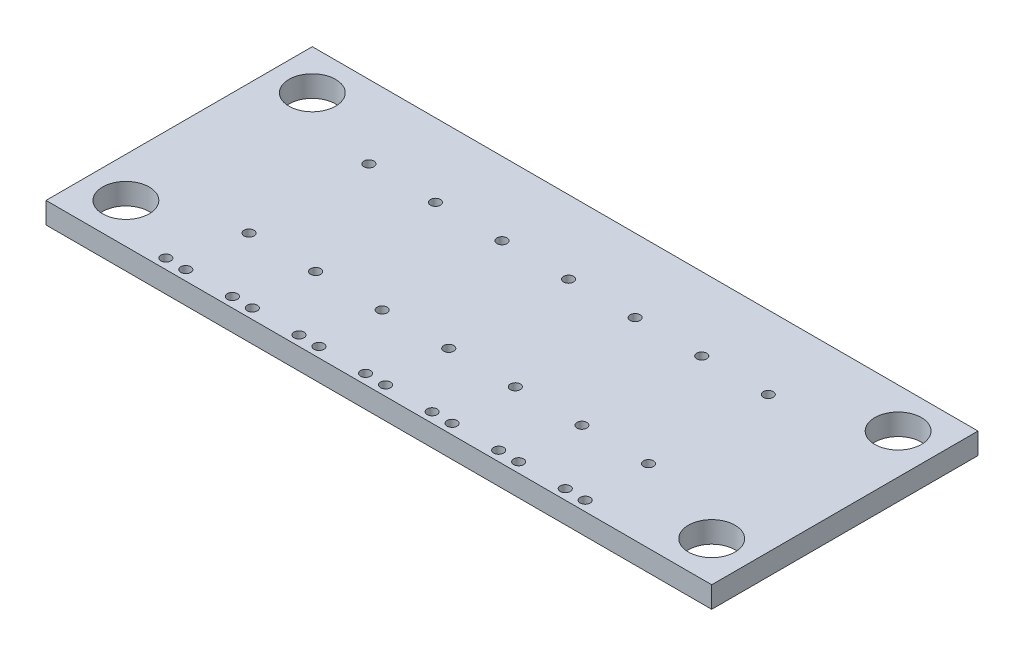
SolidWorks part; units mm, degrees
ref_plane "Front Plane" through (0, 0, 0) normal (0, 0, 1) x (1, 0, 0)
ref_plane "Top Plane" through (0, 0, 0) normal (0, 1, 0) x (1, 0, 0)
ref_plane "Right Plane" through (0, 0, 0) normal (1, 0, 0) x (0, 0, -1)
sketch "Sketch1" plane through (0, 0, 0) normal (0, 1, 0) x (1, 0, 0)
  line L1 (0, 0) -> (50, 0)
  line L2 (0, 0) -> (0, 20)
  line L3 (0, 20) -> (50, 20)
  line L4 (50, 0) -> (50, 20)
  circle A0 centre (3, 17) radius 1.75
  circle A1 centre (47, 3) radius 1.75
  circle A2 centre (3, 3) radius 1.75
  circle A3 centre (47, 17) radius 1.75
  dimension "D3" = 3.5
  dimension "D1" = 20
  dimension "D2" = 50
  dimension "D4" = 3
  dimension "D5" = 3
  dimension "D7" = 3
  dimension "D8" = 3
extrude "Boss-Extrude1" add sketch "Sketch1" along normal blind 1.6
sketch "Sketch2" plane through (0, 1.6, 0) normal (0, 1, 0) x (1, 0, 0)
  line L0 (50, 20) -> (0, 20) construction
  line L2 (7.5, 20) -> (7.5, 0)
  line L4 (10.5, 20) -> (10.5, 0)
  line L5 (0, 0) -> (50, 0) construction
  line L6 (0, 20) -> (0, 0) construction
  line L7 (9, 0) -> (9, 19.5)
  line L8 (9, 19.5) -> (7.5, 19.5)
  line L9 (10.5, 10) -> (9, 10)
  line L10 (12.5, 20) -> (12.5, 0)
  line L11 (14, 0) -> (14, 19.5)
  line L12 (15.5, 20) -> (15.5, 0)
  line L13 (15.5, 10) -> (14, 10)
  line L14 (14, 19.5) -> (12.5, 19.5)
  line L15 (17.5, 20) -> (17.5, 0)
  line L16 (19, 0) -> (19, 19.5)
  line L17 (20.5, 20) -> (20.5, 0)
  line L18 (20.5, 10) -> (19, 10)
  line L19 (19, 19.5) -> (17.5, 19.5)
  line L20 (22.5, 20) -> (22.5, 0)
  line L21 (24, 0) -> (24, 19.5)
  line L22 (25.5, 20) -> (25.5, 0)
  line L23 (25.5, 10) -> (24, 10)
  line L24 (24, 19.5) -> (22.5, 19.5)
  line L25 (27.5, 20) -> (27.5, 0)
  line L26 (29, 0) -> (29, 19.5)
  line L27 (30.5, 20) -> (30.5, 0)
  line L28 (30.5, 10) -> (29, 10)
  line L29 (29, 19.5) -> (27.5, 19.5)
  line L30 (32.5, 20) -> (32.5, 0)
  line L31 (34, 0) -> (34, 19.5)
  line L32 (35.5, 20) -> (35.5, 0)
  line L33 (35.5, 10) -> (34, 10)
  line L34 (34, 19.5) -> (32.5, 19.5)
  line L35 (37.5, 20) -> (37.5, 0)
  line L36 (39, 0) -> (39, 19.5)
  line L37 (40.5, 20) -> (40.5, 0)
  line L38 (40.5, 10) -> (39, 10)
  line L39 (39, 19.5) -> (37.5, 19.5)
  dimension "D1" = 7.5
  dimension "D2" = 3
  dimension "D3" = 1.5
  dimension "D5" = 0.5
  dimension "D6" = 10
  dimension "D4" = 7
sketch "Sketch3" plane through (0, 1.6, 0) normal (0, 1, 0) x (1, 0, 0)
  line L1 (10.5, 10) -> (9, 10) construction
  line L2 (9, 19.5) -> (7.5, 19.5) construction
  line L3 (9.75, 5.5) -> (9.75, 14.5) construction
  line L4 (8.25, 19.5) -> (8.25, 0.75) construction
  line L8 (0, 0) -> (50, 0) construction
  circle A0 centre (8.25, 0.75) radius 0.375
  circle A1 centre (9.75, 0.75) radius 0.375
  circle A2 centre (9.75, 5.5) radius 0.375
  circle A3 centre (9.75, 14.5) radius 0.375
  circle A4 centre (13.25, 0.75) radius 0.375
  circle A5 centre (14.75, 0.75) radius 0.375
  circle A6 centre (14.75, 14.5) radius 0.375
  circle A7 centre (14.75, 5.5) radius 0.375
  circle A8 centre (18.25, 0.75) radius 0.375
  circle A9 centre (19.75, 0.75) radius 0.375
  circle A10 centre (19.75, 14.5) radius 0.375
  circle A11 centre (19.75, 5.5) radius 0.375
  circle A12 centre (23.25, 0.75) radius 0.375
  circle A13 centre (24.75, 0.75) radius 0.375
  circle A14 centre (24.75, 14.5) radius 0.375
  circle A15 centre (24.75, 5.5) radius 0.375
  circle A16 centre (28.25, 0.75) radius 0.375
  circle A17 centre (29.75, 0.75) radius 0.375
  circle A18 centre (29.75, 14.5) radius 0.375
  circle A19 centre (29.75, 5.5) radius 0.375
  circle A20 centre (33.25, 0.75) radius 0.375
  circle A21 centre (34.75, 0.75) radius 0.375
  circle A22 centre (34.75, 14.5) radius 0.375
  circle A23 centre (34.75, 5.5) radius 0.375
  circle A24 centre (38.25, 0.75) radius 0.375
  circle A25 centre (39.75, 0.75) radius 0.375
  circle A26 centre (39.75, 14.5) radius 0.375
  circle A27 centre (39.75, 5.5) radius 0.375
  point P2 (0, 0)
  point P8 (8.25, 19.5)
  point P12 (9.75, 10)
  point P16 (9.75, 10)
  dimension "D1" = 0.75
  dimension "D3" = 9
  dimension "D2" = 0.75
  dimension "D4" = 7
extrude "Cut-Extrude1" cut sketch "Sketch3" against normal through all
